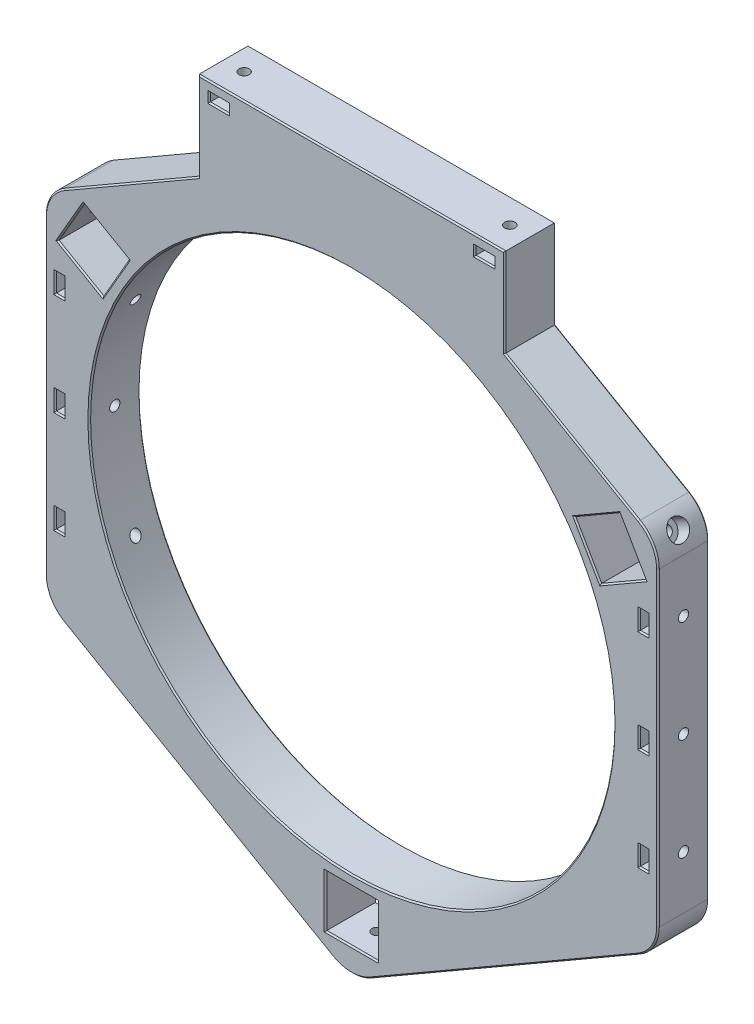
SolidWorks part; units mm, degrees
ref_plane "Top Plane" through (0, 0, 0) normal (0, 0, 1) x (1, 0, 0)
ref_plane "Front Plane" through (0, 0, 0) normal (0, 1, 0) x (1, 0, 0)
ref_plane "Right Plane" through (0, 0, 0) normal (1, 0, 0) x (0, 0, -1)
sketch "Sketch1" plane through (0, 0, 0) normal (0, 0, 1) x (1, 0, 0)
  line L0 (0, 0) -> (0, 121.7219) construction
  line L1 (0, 0) -> (107.9732, 62.3384) construction
  line L2 (0, 0) -> (110.8259, -63.9854) construction
  line L3 (0, 0) -> (0, -117.8434) construction
  line L4 (0, 0) -> (-109.5488, -63.248) construction
  line L5 (0, 0) -> (-114.2494, 65.9619) construction
  line L6 (45, 77.9423) -> (90, 51.9615)
  line L7 (90, 51.9615) -> (90, -51.9615)
  line L8 (90, -51.9615) -> (0, -103.923)
  line L9 (0, -103.923) -> (-90, -51.9615)
  line L10 (-90, -51.9615) -> (-90, 51.9615)
  line L11 (-90, 51.9615) -> (-45, 77.9423)
  line L12 (-45, 77.9423) -> (-45, 103.923)
  line L13 (-45, 103.923) -> (45, 103.923)
  line L14 (45, 103.923) -> (45, 77.9423)
  circle A0 centre (0, 0) radius 77
  circle A1 centre (0, 0) radius 103.923 construction
  dimension "D1" = 154
  dimension "D4" = 180
  dimension "D2" = 60
  dimension "D3" = 60
  dimension "D5" = 180
  dimension "D6" = 180
  dimension "D7" = 90
extrude "Boss-Extrude1" add sketch "Sketch1" along normal blind 15
sketch "Sketch2" plane through (0, 0, 15) normal (0, 0, 1) x (1, 0, 0)
  line L0 (0, 0) -> (0, -120.5827) construction
  line L1 (-7.6, -80) -> (7.6, -80)
  line L2 (-7.6, -80) -> (-7.6, -95.2)
  line L3 (-7.6, -95.2) -> (7.6, -95.2)
  line L4 (7.6, -80) -> (7.6, -95.2)
  line L5 (-7.6, -80) -> (7.6, -95.2) construction
  line L6 (-7.6, -95.2) -> (7.6, -80) construction
  line L7 (-65.482, 46.5818) -> (-73.082, 33.4182)
  line L8 (-65.482, 46.5818) -> (-78.6456, 54.1818)
  line L9 (-78.6456, 54.1818) -> (-86.2456, 41.0182)
  line L10 (-73.082, 33.4182) -> (-86.2456, 41.0182)
  line L11 (-65.482, 46.5818) -> (-86.2456, 41.0182) construction
  line L12 (-78.6456, 54.1818) -> (-73.082, 33.4182) construction
  line L13 (73.082, 33.4182) -> (65.482, 46.5818)
  line L14 (73.082, 33.4182) -> (86.2456, 41.0182)
  line L15 (86.2456, 41.0182) -> (78.6456, 54.1818)
  line L16 (65.482, 46.5818) -> (78.6456, 54.1818)
  line L17 (73.082, 33.4182) -> (78.6456, 54.1818) construction
  line L18 (86.2456, 41.0182) -> (65.482, 46.5818) construction
  point P0 (0, -87.6)
  point P8 (-75.8638, 43.8)
  point P15 (75.8638, 43.8)
  point P20 (0, 0)
  dimension "D1" = 80
  dimension "D2" = 15.2
  dimension "D3" = 15.2
  dimension "D4" = 3
extrude "Cut-Extrude1" cut sketch "Sketch2" against normal through all
fillet "Fillet1" radius 11.11 5 edges at (-90, -51.9615, 7.5) (-90, 51.9615, 7.5) (90, 51.9615, 7.5) (90, -51.9615, 7.5) (0, -103.923, 7.5)
ref_plane "Plane1" through (0, 0, 0) normal (-0.866, 0.5, 0) x (0, 0, -1)
sketch "Sketch9" plane through (-82.4456, 47.6, 0) normal (0.866, -0.5, 0) x (0, 0, -1)
  line L0 (0, 0) -> (-36.7336, 0) construction
  line L2 (-15, 7.6) -> (-15, -7.6) construction
  circle A0 centre (-7.5, 0) radius 1.5
  dimension "D1" = 3
  dimension "D2" = 7.5
extrude "Cut-Extrude6" cut sketch "Sketch9" against normal blind 3
sketch "Sketch10" plane through (-85.0437, 49.1, 0) normal (0.866, -0.5, 0) x (0, 0, -1)
  circle A0 centre (-7.5, 0) radius 3
  dimension "D1" = 6
extrude "Cut-Extrude7" cut sketch "Sketch10" against normal through all
pattern_circular "CirPattern2" count 3 over 360 about axis through (0, 0, 0) along (0, 0, 1) of "Cut-Extrude6", "Cut-Extrude7"
sketch "Sketch15" plane through (0, 103.923, 0) normal (0, 1, 0) x (1, 0, 0)
  line L0 (0, 0) -> (0, -22.7358) construction
  line L1 (45, 0) -> (-45, 0) construction
  circle A0 centre (-39, -7.5) radius 1.5
  circle A1 centre (39, -7.5) radius 1.5
  dimension "D5" = 3
  dimension "D1" = 39
  dimension "D2" = 39
  dimension "D3" = 7.5
  dimension "D4" = 7.5
extrude "Cut-Extrude11" cut sketch "Sketch15" against normal blind 30
sketch "Sketch16" plane through (0, 0, 15) normal (0, 0, 1) x (1, 0, 0)
  line L0 (-39, 104.8943) -> (-39, 97.148) construction
  line L1 (-41.8, 100.923) -> (-36.2, 100.923)
  line L2 (-41.8, 100.923) -> (-41.8, 98.423)
  line L3 (-41.8, 98.423) -> (-36.2, 98.423)
  line L4 (-36.2, 100.923) -> (-36.2, 98.423)
  line L5 (-37.5, 73.923) -> (-37.5, 103.923) construction
  line L6 (-40.5, 103.923) -> (-40.5, 73.923) construction
  line L7 (45, 103.923) -> (-45, 103.923) construction
  line L8 (0, -8.25) -> (0, 8.25) construction
  line L9 (36.2, 100.923) -> (36.2, 98.423)
  line L10 (41.8, 98.423) -> (36.2, 98.423)
  line L11 (41.8, 100.923) -> (41.8, 98.423)
  line L12 (41.8, 100.923) -> (36.2, 100.923)
  point P10 (-39, 100.923)
  dimension "D1" = 2.5
  dimension "D2" = 5.6
  dimension "D3" = 3
extrude "Cut-Extrude12" cut sketch "Sketch16" against normal through all
sketch "Sketch18" plane through (90, 0, 0) normal (1, 0, 0) x (0, 0, -1)
  line L0 (-7.5, 42.4433) -> (-7.5, -42.4433) construction
  line L1 (0, 0) -> (-19.0216, 0) construction
  line L2 (0, -45.5472) -> (0, 45.5472) construction
  circle A0 centre (-7.5, 30) radius 1.5
  circle A1 centre (-7.5, 0) radius 1.5
  circle A2 centre (-7.5, -30) radius 1.5
  dimension "D1" = 3
  dimension "D2" = 30
  dimension "D3" = 30
  dimension "D4" = 7.5
extrude "Cut-Extrude13" cut sketch "Sketch18" against normal through all
sketch "Sketch19" plane through (0, 0, 15) normal (0, 0, 1) x (1, 0, 0)
  line L0 (-92.2712, 30) -> (-78.4936, 30) construction
  line L1 (-92.2712, 0) -> (-81.7063, 0) construction
  line L2 (-70.262, 31.5) -> (-90, 31.5) construction
  line L3 (-87, 32.8) -> (-84.5, 32.8)
  line L4 (-87, 32.8) -> (-87, 27.2)
  line L5 (-87, 27.2) -> (-84.5, 27.2)
  line L6 (-84.5, 32.8) -> (-84.5, 27.2)
  line L7 (-87, 2.8) -> (-84.5, 2.8)
  line L8 (-87, 2.8) -> (-87, -2.8)
  line L9 (-87, -2.8) -> (-84.5, -2.8)
  line L10 (-84.5, 2.8) -> (-84.5, -2.8)
  line L11 (-90, 28.5) -> (-71.5315, 28.5) construction
  line L13 (-90, 45.5472) -> (-90, -45.5472) construction
  line L14 (8.25, 0) -> (-8.25, 0) construction
  line L15 (-92.2712, -30) -> (-78.4936, -30) construction
  line L16 (-84.5, -32.8) -> (-84.5, -27.2)
  line L17 (-87, -27.2) -> (-84.5, -27.2)
  line L18 (-87, -32.8) -> (-87, -27.2)
  line L19 (-87, -32.8) -> (-84.5, -32.8)
  line L20 (0, -8.25) -> (0, 8.25) construction
  line L21 (92.2712, -30) -> (78.4936, -30) construction
  line L22 (92.2712, 0) -> (81.7063, 0) construction
  line L23 (92.2712, 30) -> (78.4936, 30) construction
  line L24 (87, -32.8) -> (84.5, -32.8)
  line L25 (87, -32.8) -> (87, -27.2)
  line L26 (87, -27.2) -> (84.5, -27.2)
  line L27 (84.5, -32.8) -> (84.5, -27.2)
  line L28 (84.5, 2.8) -> (84.5, -2.8)
  line L29 (87, -2.8) -> (84.5, -2.8)
  line L30 (87, 2.8) -> (87, -2.8)
  line L31 (87, 2.8) -> (84.5, 2.8)
  line L32 (84.5, 32.8) -> (84.5, 27.2)
  line L33 (87, 27.2) -> (84.5, 27.2)
  line L34 (87, 32.8) -> (87, 27.2)
  line L35 (87, 32.8) -> (84.5, 32.8)
  dimension "D1" = 5.6
  dimension "D2" = 2.5
  dimension "D3" = 3
extrude "Cut-Extrude14" cut sketch "Sketch19" against normal through all
chamfer "Chamfer1" distance 0.4 angle 45 118 edges at (0, -102.2043, 0) (45, -77.9423, 0) (88.5115, -51.1022, 0) (90, 0, 0) (88.5115, 51.1022, 0) (64.7225, 66.5555, 0) (-64.7225, 66.5555, 0) (-88.5115, 51.1022, 0) (-90, 0, 0) (-88.5115, -51.1022, 0) (-45, -77.9423, 0) (82.4456, 47.6, 0) (79.6638, 37.2182, 0) (69.282, 40, 0) (72.0638, 50.3818, 0) (-82.4456, 47.6, 0) (-72.0638, 50.3818, 0) (-69.282, 40, 0) (-79.6638, 37.2182, 0) (0, -95.2, 0) (-7.6, -87.6, 0) (0, -80, 0) (7.6, -87.6, 0) (77, 0, 0) (77, 0, 15) (-88.5115, 51.1022, 15) (-64.7225, 66.5555, 15) (64.7225, 66.5555, 15) (88.5115, 51.1022, 15) (90, 0, 15) (88.5115, -51.1022, 15) (45, -77.9423, 15) (0, -102.2043, 15) (-45, -77.9423, 15) (-88.5115, -51.1022, 15) (-90, 0, 15) (79.6638, 37.2182, 15) (82.4456, 47.6, 15) (72.0638, 50.3818, 15) (69.282, 40, 15) (-72.0638, 50.3818, 15) (-82.4456, 47.6, 15) (-79.6638, 37.2182, 15) (-69.282, 40, 15) (-7.6, -87.6, 15) (0, -95.2, 15) (7.6, -87.6, 15) (0, -80, 15) (-45, 90.9327, 15) (0, 103.923, 15) (45, 90.9327, 15) (45, 90.9327, 0) (0, 103.923, 0) (-45, 90.9327, 0) (39, 98.423, 15) (41.8, 99.673, 15) (39, 100.923, 15) (36.2, 99.673, 15) (-36.2, 99.673, 15) (-39, 100.923, 15) (-41.8, 99.673, 15) (-39, 98.423, 15) (41.8, 99.673, 0) (39, 98.423, 0) (36.2, 99.673, 0) (39, 100.923, 0) (-39, 100.923, 0) (-36.2, 99.673, 0) (-39, 98.423, 0) (-41.8, 99.673, 0) (-84.5, 30, 15) (-85.75, 32.8, 15) (-87, 30, 15) (-85.75, 27.2, 15) (-84.5, 0, 15) (-85.75, 2.8, 15) (-87, 0, 15) (-85.75, -2.8, 15) (-85.75, -27.2, 15) (-87, -30, 15) (-85.75, -32.8, 15) (-84.5, -30, 15) (84.5, -30, 15) (85.75, -32.8, 15) (87, -30, 15) (85.75, -27.2, 15) (85.75, -2.8, 15) (87, 0, 15) (85.75, 2.8, 15) (84.5, 0, 15) (85.75, 27.2, 15) (87, 30, 15) (85.75, 32.8, 15) (84.5, 30, 15) (-85.75, 32.8, 0) (-84.5, 30, 0) (-85.75, 27.2, 0) (-87, 30, 0) (-85.75, 2.8, 0) (-84.5, 0, 0) (-85.75, -2.8, 0) (-87, 0, 0) (-87, -30, 0) (-85.75, -27.2, 0) (-84.5, -30, 0) (-85.75, -32.8, 0) (85.75, -32.8, 0) (84.5, -30, 0) (85.75, -27.2, 0) (87, -30, 0) (87, 0, 0) (85.75, -2.8, 0) (84.5, 0, 0) (85.75, 2.8, 0) (87, 30, 0) (85.75, 27.2, 0) (84.5, 30, 0) (85.75, 32.8, 0)
